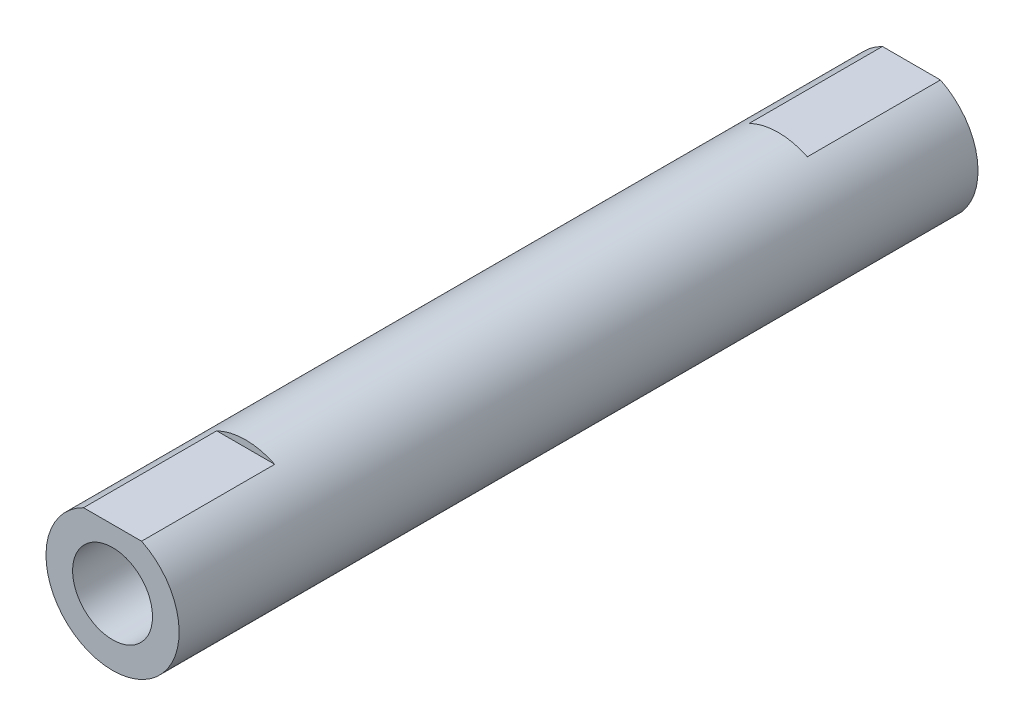
SolidWorks part; units mm, degrees
ref_plane "Front Plane" through (0, 0, 0) normal (0, 0, 1) x (1, 0, 0)
ref_plane "Top Plane" through (0, 0, 0) normal (0, 1, 0) x (1, 0, 0)
ref_plane "Right Plane" through (0, 0, 0) normal (1, 0, 0) x (0, 0, -1)
sketch "Sketch1" plane through (0, 0, 0) normal (0, 0, 1) x (1, 0, 0)
  circle A0 centre (0, 0) radius 5
  circle A1 centre (0, 0) radius 3
  dimension "D1" = 10
  dimension "D2" = 6
extrude "Boss-Extrude1" add sketch "Sketch1" along normal mid plane 60
sketch "Sketch4" plane through (0, 0, 30) normal (0, 0, 1) x (1, 0, 0)
  line L0 (-2.1794, 4.5) -> (2.1794, 4.5)
  circle A0 centre (0, 0) radius 5 construction
  arc A1 (2.1794, 4.5) -> (-2.1794, 4.5) centre (0, 0) ccw
  dimension "D1" = 4.5
extrude "Cut-Extrude1" cut sketch "Sketch4" against normal blind 10 and the other way through all
mirror "Mirror3" about plane through (0, 0, 0) normal (0, 0, 1) of "Cut-Extrude1"
